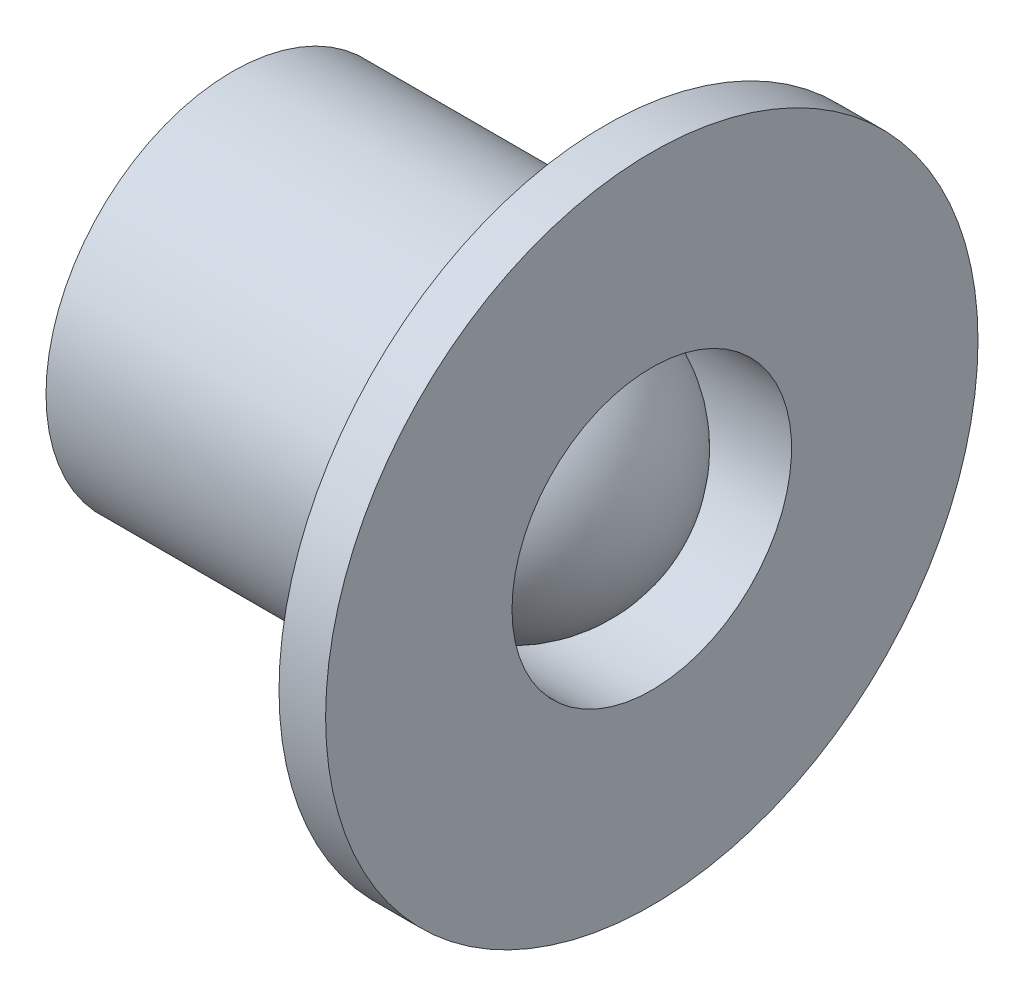
SolidWorks part; units mm, degrees
ref_plane "Plan de face" through (0, 0, 0) normal (0, 0, 1) x (1, 0, 0)
ref_plane "Plan de dessus" through (0, 0, 0) normal (0, 1, 0) x (1, 0, 0)
ref_plane "Plan de droite" through (0, 0, 0) normal (1, 0, 0) x (0, 0, -1)
sketch "Esquisse1" plane through (0, 0, 0) normal (0, 0, 1) x (1, 0, 0)
  line L0 (0, 0) -> (25.6071, 0) construction
  line L1 (0, 1.5) -> (0, 3.5)
  line L2 (0, 3.5) -> (-0.5, 3.5)
  line L3 (-0.5, 3.5) -> (-0.5, 2)
  line L4 (0, 1.5) -> (-1.5, 1.5)
  line L5 (0, 1.5) -> (0, 0) construction
  line L8 (-0.5, 2) -> (-4.5, 2)
  line L9 (-4.5, 2) -> (-4.5, 0)
  line L10 (-4.5, 0) -> (0, 0)
  arc A0 (0, 0) -> (-1.5, 1.5) centre (-1.5, 0) ccw
  dimension "D6" = 1.5
  dimension "D1" = 7
  dimension "D2" = 4
  dimension "D3" = 4
  dimension "D4" = 0.5
  dimension "D5" = 3
revolve "Révolution1" add sketch "Esquisse1" angle 360 about L0
